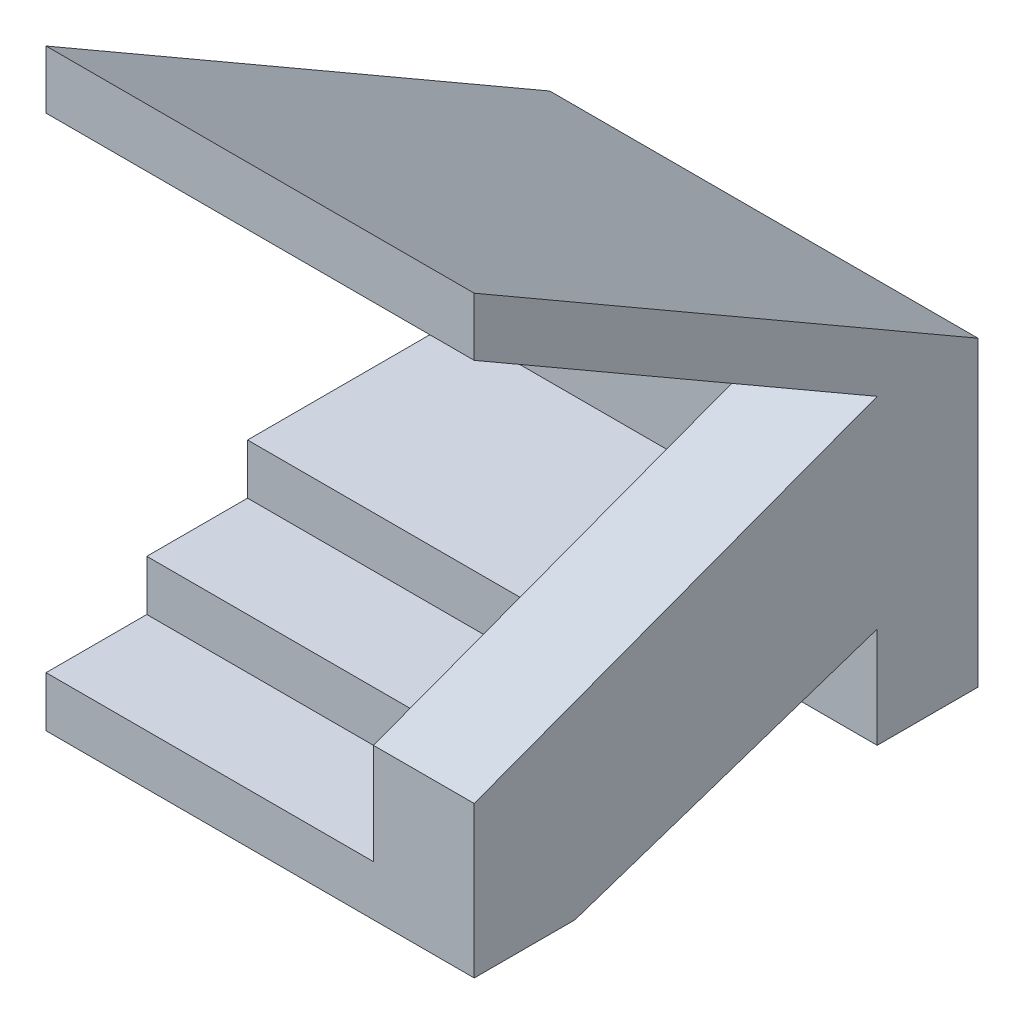
SolidWorks part; units mm, degrees
ref_plane "Front Plane" through (0, 0, 0) normal (0, 0, 1) x (1, 0, 0)
ref_plane "Top Plane" through (0, 0, 0) normal (0, 1, 0) x (1, 0, 0)
ref_plane "Right Plane" through (0, 0, 0) normal (1, 0, 0) x (0, 0, -1)
sketch "Sketch1" plane through (0, 0, 0) normal (1, 0, 0) x (0, 0, -1)
  line L0 (0, 0) -> (0, 10)
  line L1 (0, 10) -> (20, 10)
  line L2 (20, 10) -> (20, 20)
  line L3 (20, 20) -> (40, 20)
  line L4 (40, 20) -> (40, 30)
  line L5 (40, 30) -> (80, 30)
  line L6 (0, 0) -> (20, 0)
  line L7 (20, 0) -> (80, 20)
  line L8 (80, 20) -> (80, 0)
  line L9 (80, 0) -> (100, 0)
  line L10 (100, 0) -> (100, 60)
  line L11 (100, 60) -> (0, 117.735)
  line L12 (0, 117.735) -> (0, 106.188)
  line L13 (0, 106.188) -> (80, 60)
  line L14 (80, 60) -> (80, 30)
  dimension "D1" = 10
  dimension "D2" = 10
  dimension "D3" = 10
  dimension "D4" = 20
  dimension "D5" = 60
  dimension "D6" = 20
  dimension "D7" = 20
  dimension "D8" = 120
  dimension "D9" = 60
extrude "Steps" add sketch "Sketch1" along normal blind 85
sketch "Sketch2" plane through (85, 0, 0) normal (1, 0, 0) x (0, 0, -1)
  line L0 (0, 0) -> (0, 30)
  line L1 (0, 30) -> (80, 60)
  line L2 (80, 60) -> (100, 60)
  line L3 (100, 60) -> (100, 0)
  line L4 (0, 0) -> (20, 0)
  line L5 (20, 0) -> (80, 20)
  line L6 (80, 20) -> (80, 0)
  line L7 (80, 0) -> (100, 0)
extrude "Side wall" add sketch "Sketch2" against normal blind 20
